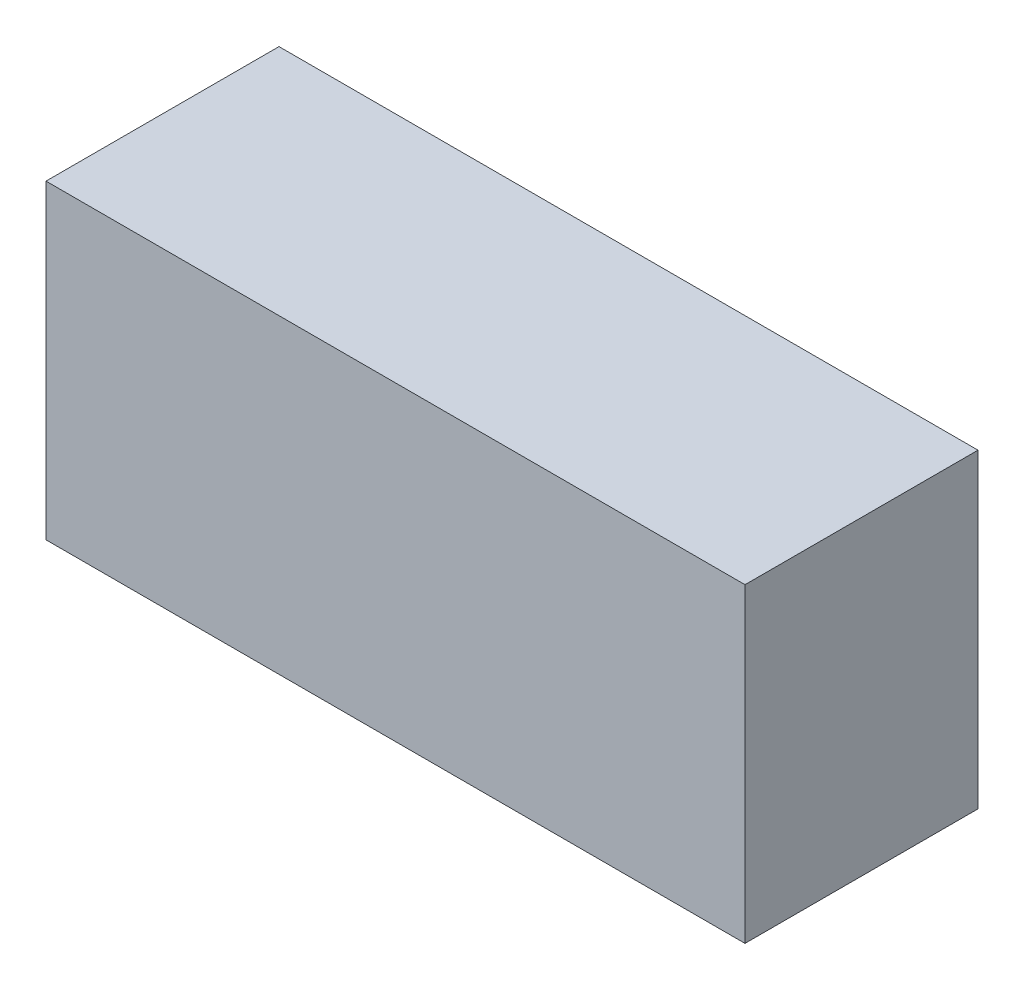
SolidWorks part; units mm, degrees
material "Custom Plastic"
ref_plane "Front Plane" through (0, 0, 0) normal (0, 0, 1) x (1, 0, 0)
ref_plane "Top Plane" through (0, 0, 0) normal (0, 1, 0) x (1, 0, 0)
ref_plane "Right Plane" through (0, 0, 0) normal (1, 0, 0) x (0, 0, -1)
sketch "Sketch1" plane through (0, 0, 0) normal (0, 0, 1) x (1, 0, 0)
  line L1 (-60.8405, -21.5548) -> (-51.8405, -21.5548)
  line L2 (-60.8405, -21.5548) -> (-60.8405, -17.5548)
  line L3 (-60.8405, -17.5548) -> (-51.8405, -17.5548)
  line L4 (-51.8405, -21.5548) -> (-51.8405, -17.5548)
  dimension "D1" = 9
  dimension "D2" = 4
extrude "Boss-Extrude1" add sketch "Sketch1" along normal blind 3
